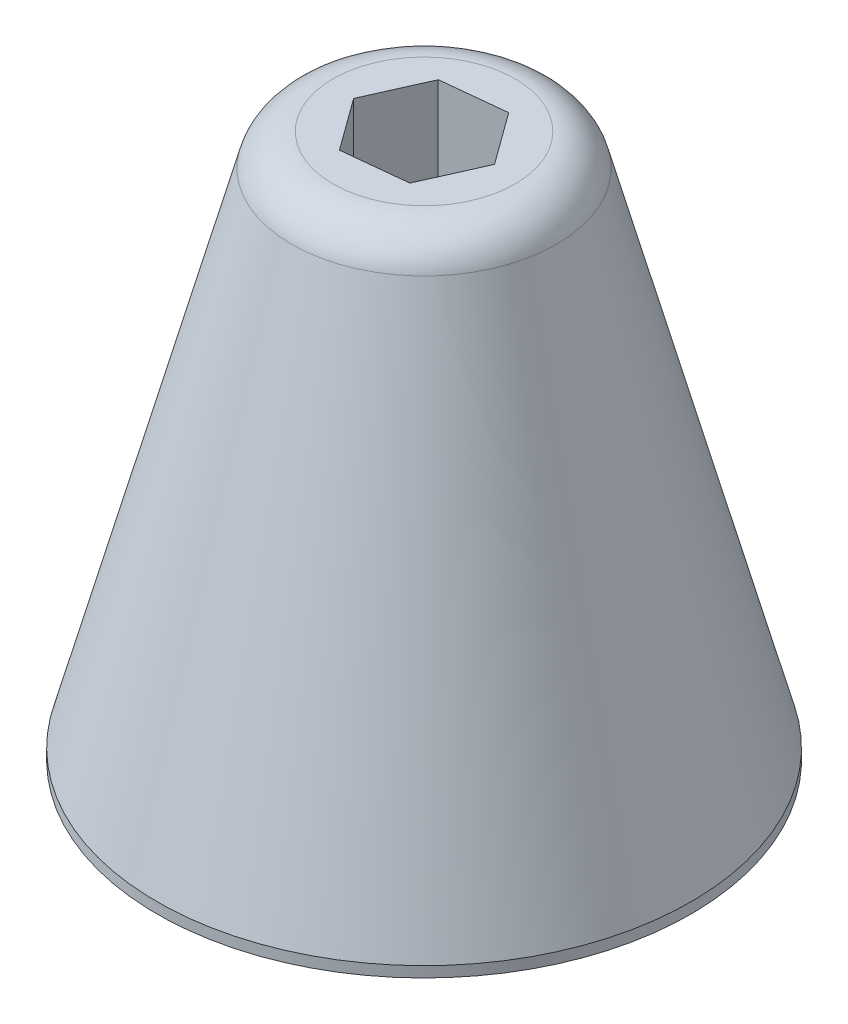
SolidWorks part; units mm, degrees
ref_plane "Front Plane" through (0, 0, 0) normal (0, 0, 1) x (1, 0, 0)
ref_plane "Top Plane" through (0, 0, 0) normal (0, 1, 0) x (1, 0, 0)
ref_plane "Right Plane" through (0, 0, 0) normal (1, 0, 0) x (0, 0, -1)
sketch "Sketch2" plane through (0, 0, 0) normal (0, 1, 0) x (1, 0, 0)
  circle A0 centre (0, 0) radius 31.75
extrude "Boss-Extrude1" add sketch "Sketch2" along normal blind 63.5 draft 15 contours A0
sketch "Sketch3" plane through (0, 0, 0) normal (0, -1, 0) x (1, 0, 0)
  circle A0 centre (0, 0) radius 31.75
extrude "Boss-Extrude2" add sketch "Sketch3" along normal blind 1.27
sketch "Sketch7" plane through (0, 0, 0) normal (0, 1, 0) x (1, 0, 0)
  line L1 (4.4828, -6.1689) -> (7.5838, 0.7978)
  line L2 (7.5838, 0.7978) -> (3.101, 6.9667)
  line L3 (3.101, 6.9667) -> (-4.4828, 6.1689)
  line L4 (-4.4828, 6.1689) -> (-7.5838, -0.7978)
  line L5 (-7.5838, -0.7978) -> (-3.101, -6.9667)
  line L6 (-3.101, -6.9667) -> (4.4828, -6.1689)
  circle A0 centre (0, 0) radius 6.604 construction
extrude "Cut-Extrude2" cut sketch "Sketch7" against normal through all both and the other way through all
fillet "Fillet1" radius 5.08 1 edges at (0, 63.5, 14.7352)
